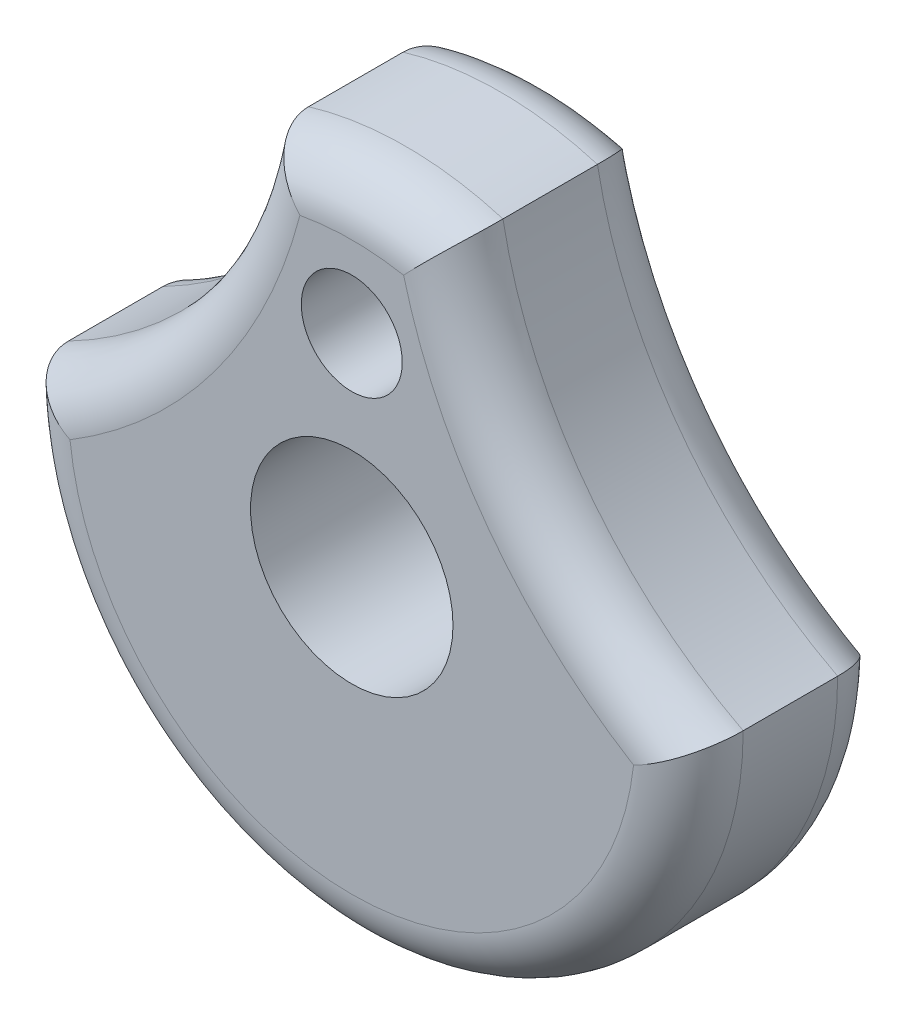
SolidWorks part; units mm, degrees
ref_plane "Front Plane" through (0, 0, 0) normal (0, 0, 1) x (1, 0, 0)
ref_plane "Top Plane" through (0, 0, 0) normal (0, 1, 0) x (1, 0, 0)
ref_plane "Right Plane" through (0, 0, 0) normal (1, 0, 0) x (0, 0, -1)
sketch "Sketch1" plane through (0, 0, 0) normal (0, 0, 1) x (1, 0, 0)
  arc A0 (4.5728, 15.2021) -> (-4.5728, 15.2021) centre (0, 0) ccw
  arc A3 (4.5728, 15.2021) -> (15.875, 0) centre (25.7938, 19.1767) ccw
  arc A4 (-4.5728, 15.2021) -> (-15.875, 0) centre (-25.7938, 19.1767) cw
  arc A5 (-15.875, 0) -> (15.875, 0) centre (0, 0) ccw
extrude "Boss-Extrude1" add sketch "Sketch1" along normal blind 9.525
sketch "Sketch2" plane through (0, 0, 9.525) normal (0, 0, 1) x (1, 0, 0)
  line L0 (0, 0) -> (0, 9.525)
  circle A0 centre (0, 0) radius 4.7625
  circle A1 centre (0, 9.525) radius 2.3749
extrude "Cut-Extrude1" cut sketch "Sketch2" against normal blind 9.525
fillet "Fillet1" radius 2.54 8 edges at (0, -15.875, 0) (0, 15.875, 0) (-8.4676, 6.2953, 0) (8.4676, 6.2953, 0) (0, -15.875, 9.525) (-8.4676, 6.2953, 9.525) (0, 15.875, 9.525) (8.4676, 6.2953, 9.525)
